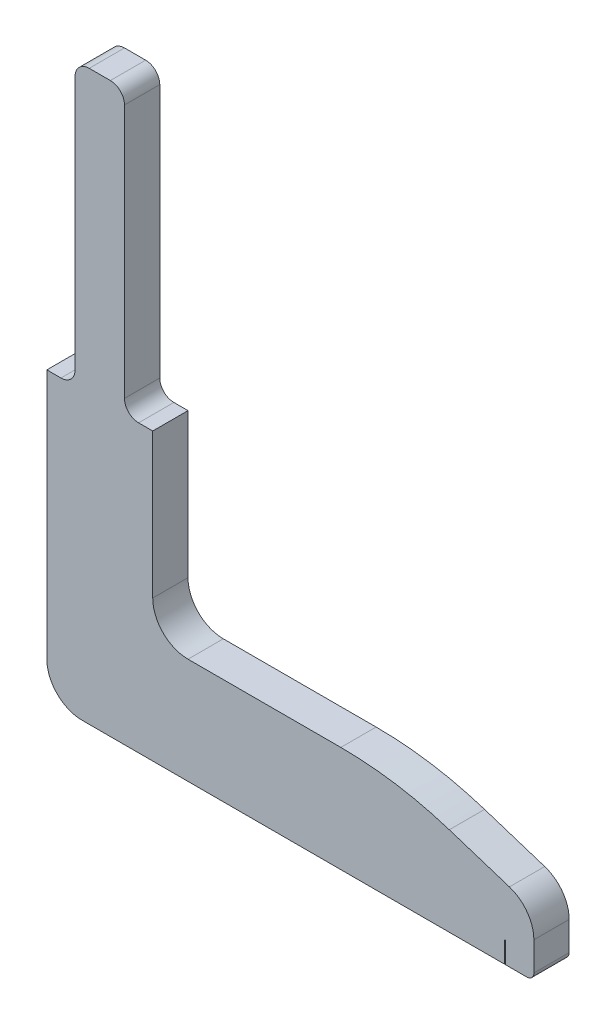
SolidWorks part; units mm, degrees
ref_plane "Front Plane" through (0, 0, 0) normal (0, 0, 1) x (1, 0, 0)
ref_plane "Top Plane" through (0, 0, 0) normal (0, 1, 0) x (1, 0, 0)
ref_plane "Right Plane" through (0, 0, 0) normal (1, 0, 0) x (0, 0, -1)
sketch "Sketch1" plane through (0, 0, 0) normal (0, 0, 1) x (1, 0, 0)
  line L0 (0, -1) -> (0, -35.5)
  line L1 (5, -40.5) -> (68, -40.5)
  line L2 (69, -39.5) -> (69, -35.43)
  line L3 (41.65, -25.5) -> (20, -25.5)
  line L4 (15, -20.5) -> (15, -1)
  line L5 (14, 0) -> (11, 0)
  line L6 (15, -1) -> (15, 0)
  line L7 (15, 0) -> (14, 0)
  line L8 (0, -1) -> (0, 0)
  line L9 (0, 0) -> (1, 0)
  line L10 (65.5369, -30.6721) -> (57.0187, -27.9206)
  line L11 (4, 0) -> (4, 40)
  line L12 (11, 0) -> (11, 40)
  line L13 (11, 40) -> (4, 40)
  line L14 (4, 0) -> (1, 0)
  arc A2 (69, -39.5) -> (68, -40.5) centre (68, -39.5) cw
  arc A4 (5, -40.5) -> (0, -35.5) centre (5, -35.5) cw
  arc A5 (15, -20.5) -> (20, -25.5) centre (20, -20.5) ccw
  arc A6 (65.5369, -30.6721) -> (69, -35.43) centre (64, -35.43) cw
  arc A7 (41.65, -25.5) -> (57.0187, -27.9206) centre (41.65, -75.5) cw
  point P9 (0, 0)
  point P12 (15, 0)
  point P15 (69, -40.5)
  point P18 (69, -25.5)
  point P21 (0, -40.5)
  point P24 (15, -25.5)
  dimension "D6" = 5
  dimension "D5" = 5
  dimension "D7" = 50
  dimension "D1" = 25.5
  dimension "D2" = 15
  dimension "D3" = 69
  dimension "D4" = 15
  dimension "D8" = 4
  dimension "D9" = 4
  dimension "D10" = 40
extrude "Boss-Extrude1" add sketch "Sketch1" along normal blind 5
sketch "Sketch2" plane through (0, -40.5, 0) normal (0, -1, 0) x (1, 0, 0)
  line L0 (0, 2.5) -> (64.9, 2.5) construction
  line L1 (0, 5) -> (0, 0) construction
  line L2 (5, 5) -> (68, 5) construction
  line L3 (64.85, 0) -> (64.95, 0)
  line L4 (64.85, 0) -> (64.85, 5)
  line L5 (64.85, 5) -> (64.95, 5)
  line L6 (64.95, 0) -> (64.95, 5)
  line L7 (64.85, 0) -> (64.95, 5) construction
  line L8 (64.85, 5) -> (64.95, 0) construction
  dimension "D1" = 64.9
  dimension "D2" = 0.1
extrude "Cut-Extrude2" cut sketch "Sketch2" against normal blind 3
fillet "Fillet1" radius 2 4 edges at (4, 40, 2.5) (11, 40, 2.5) (4, 0, 2.5) (11, 0, 2.5)
equation "\"A.L\"= 0.07m"
equation "\"A.h\"= 0.007m"
equation "\"A.d\"= 0.005m"
equation "\"A.delta\"= 45.0001"
equation "\"A.w\"= 0m"
equation "\"A.v\"= 0.013m"
equation "\"A.s\"= 0.014m"
equation "\"A.t\"= 0.007m"
equation "\"B.L\"= 0.065m"
equation "\"B.h\"= 0.008m"
equation "\"B.s\"= 0.016m"
equation "\"B.t\"= 0.008m"
equation "\"C.h\"= 0.0065m"
equation "\"C.d\"= 0.005m"
equation "\"C.L\"= 0.05m"
equation "\"C.wmax\"= 0.003m"
equation "\"D.L\"= 0.06m"
equation "\"D.h\"= 0.008m"
equation "\"D.s\"= 0.012m"
equation "\"D.t\"= 0.008m"
equation "\"a_h\"= 0.0001m"
equation "\"a_d\"= 0.005m"
equation "\"a_L\"= 0.008m"
equation "\"b_h\"= 0.0004m"
equation "\"b_d\"= 0.005m"
equation "\"b_L\"= 0.008m"
equation "\"c_h\"= 0.0001m"
equation "\"c_d\"= 0.005m"
equation "\"c_L\"= 0.01m"
equation "\"d_h\"= 0.0001m"
equation "\"d_d\"= 0.005m"
equation "\"d_L\"= 0.01m"
equation "\"S.h\"= 0.015m"
equation "\"S.L\"= 0.09175m"
equation "\"D1@Sketch1\"=\"S.L\"-\"C.wmax\"-\"C.h\"/2-60mm"
equation "\"D2@Sketch1\"=\"S.h\""
equation "\"D3@Sketch1\"=\"C.L\"+\"S.h\"+0.004"
equation "\"D4@Sketch1\"=\"S.h\""
equation "\"D1@Boss-Extrude1\"=0.005m"
equation "\"D1@Sketch2\"=\"C.L\"+\"S.h\"-\"d_h\""
equation "\"D2@Sketch2\"=\"d_h\""
